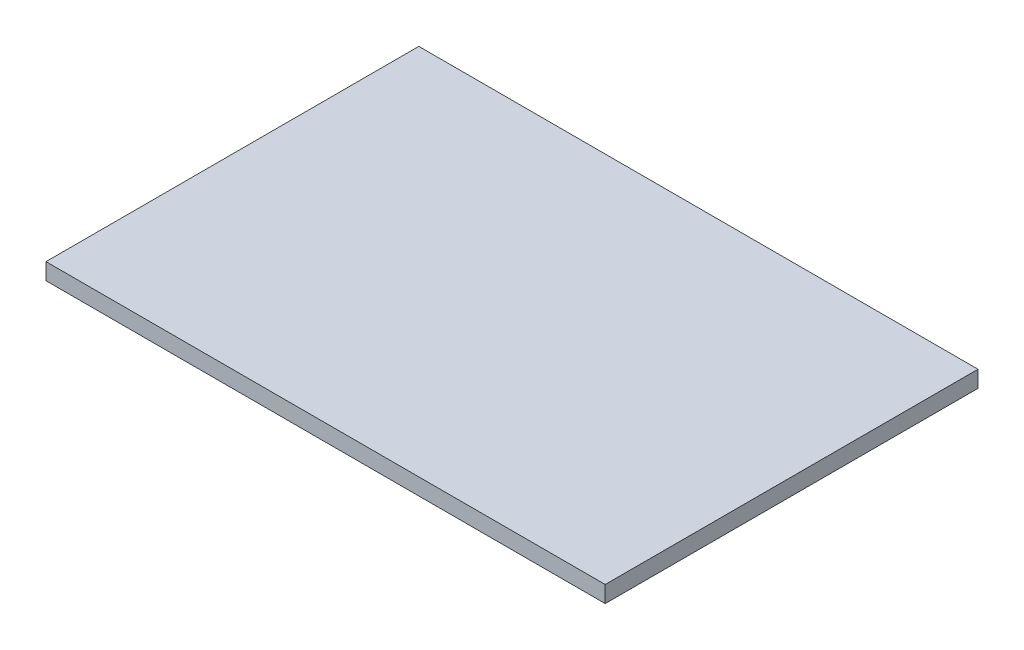
SolidWorks part; units mm, degrees
ref_plane "Front Plane" through (0, 0, 0) normal (0, 0, 1) x (1, 0, 0)
ref_plane "Top Plane" through (0, 0, 0) normal (0, 1, 0) x (1, 0, 0)
ref_plane "Right Plane" through (0, 0, 0) normal (1, 0, 0) x (0, 0, -1)
sketch "Sketch1" plane through (0, 0, 0) normal (0, 1, 0) x (1, 0, 0)
  line L1 (42.8625, -28.575) -> (-42.8625, -28.575)
  line L2 (42.8625, -28.575) -> (42.8625, 28.575)
  line L3 (42.8625, 28.575) -> (-42.8625, 28.575)
  line L4 (-42.8625, -28.575) -> (-42.8625, 28.575)
  line L5 (42.8625, -28.575) -> (-42.8625, 28.575) construction
  line L6 (42.8625, 28.575) -> (-42.8625, -28.575) construction
  point P0 (0, 0)
  dimension "D1" = 85.725
  dimension "D2" = 57.15
extrude "Boss-Extrude1" add sketch "Sketch1" along normal blind 2.54
sketch "Sketch2" plane through (0, 2.54, 0) normal (0, 1, 0) x (1, 0, 0)
  line L0 (-42.8625, 0) -> (42.8625, 0) construction
  line L1 (-42.8625, 28.575) -> (-42.8625, -28.575) construction
  line L2 (42.8625, -28.575) -> (42.8625, 28.575) construction
  line L3 (0, 28.575) -> (0, -28.575) construction
  line L4 (42.8625, 28.575) -> (-42.8625, 28.575) construction
  line L5 (-42.8625, -28.575) -> (42.8625, -28.575) construction
  line L14 (-36.5125, -22.225) -> (36.5125, -22.225)
  line L15 (36.5125, -22.225) -> (36.5125, 22.225)
  line L16 (-36.5125, 22.225) -> (-36.5125, -22.225)
  line L17 (36.5125, 22.225) -> (-36.5125, 22.225)
  line L18 (-36.5125, -22.225) -> (36.5125, -22.225) construction
  line L19 (36.5125, -22.225) -> (36.5125, 22.225) construction
  line L20 (-36.5125, 22.225) -> (-36.5125, -22.225) construction
  line L21 (36.5125, 22.225) -> (-36.5125, 22.225) construction
  ellipse E0 centre (0, 0) end of major axis (-36.5125, 0) minor radius 22.225
  point P13 (-34.4167, -7.4214)
  point P19 (-29.3024, -13.2597)
  point P20 (-22.7112, -17.4023)
  point P21 (-15.4173, -20.1465)
  point P22 (-7.7805, -21.7145)
  point P23 (0, -22.225)
  point P24 (7.7805, -21.7145)
  point P25 (15.4173, -20.1465)
  point P28 (22.7113, -17.4023)
  point P29 (29.3024, -13.2597)
  point P30 (34.4167, -7.4214)
  point P31 (36.5125, 0)
  point P32 (34.4167, 7.4214)
  point P33 (29.3024, 13.2597)
  point P34 (22.7112, 17.4023)
  point P35 (15.4173, 20.1465)
  point P36 (7.7805, 21.7145)
  point P37 (0, 22.225)
  point P38 (-7.7805, 21.7145)
  point P39 (-15.4173, 20.1465)
  point P40 (-22.7113, 17.4023)
  point P41 (-29.3024, 13.2597)
  point P42 (-34.4167, 7.4214)
  point P43 (-36.5125, 0)
  dimension "D3" = 6.35
